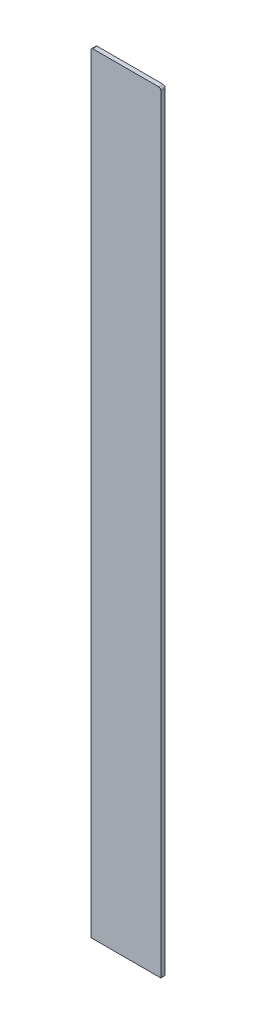
SolidWorks part; units mm, degrees
ref_plane "Front Plane" through (0, 0, 0) normal (0, 0, 1) x (1, 0, 0)
ref_plane "Top Plane" through (0, 0, 0) normal (0, 1, 0) x (1, 0, 0)
ref_plane "Right Plane" through (0, 0, 0) normal (1, 0, 0) x (0, 0, -1)
sketch "Sketch1" plane through (0, 0, 0) normal (0, 0, 1) x (1, 0, 0)
  line L0 (-2.75, -2.75) -> (-2.75, -84)
  line L1 (-2.75, -2.75) -> (2.75, -2.75)
  line L2 (-2.75, -2.75) -> (-2.75, 2.75)
  line L3 (-2.75, 2.75) -> (2.75, 2.75)
  line L4 (2.75, -2.75) -> (2.75, 2.75)
  line L5 (-2.75, -2.75) -> (2.75, 2.75) construction
  line L6 (-2.75, 2.75) -> (2.75, -2.75) construction
  line L7 (-4, -4) -> (4, -4)
  line L8 (-4, -4) -> (-4, 4)
  line L9 (-4, 4) -> (4, 4)
  line L10 (4, -4) -> (4, 4)
  line L11 (-4, -4) -> (4, 4) construction
  line L12 (-4, 4) -> (4, -4) construction
  line L13 (-4, -4) -> (4, -4)
  line L14 (-4, -4) -> (-4, -84)
  line L15 (-4, -84) -> (4, -84)
  line L16 (4, -4) -> (4, -84)
  line L17 (2.75, -2.75) -> (2.75, -84)
  point P0 (0, 0)
  point P5 (0, 0)
  dimension "D1" = 5.5
  dimension "D2" = 8
  dimension "D3" = 80
  dimension "D4" = 8
extrude "Boss-Extrude1" add sketch "Sketch1" along normal blind 0.105 contours L13 L17 L15 L16 | L4 L17 L13 L10 L9 L8 L7 L0 L2 L3 | L14 L15 L0 L7
fillet "Fillet1" radius 0.25 4 edges at (-4, 4, 0.0525) (4, 4, 0.0525) (-2.75, 2.75, 0.0525) (2.75, 2.75, 0.0525)
sketch "Sketch2" plane through (0, 0, 0) normal (0, 0, -1) x (-1, 0, 0)
  line L0 (-2.75, -84) -> (2.75, -84)
  line L8 (4, -84) -> (4, 3.75)
  line L9 (3.75, 4) -> (-3.75, 4)
  line L10 (-4, 3.75) -> (-4, -84)
  line L11 (-4, -84) -> (-2.75, -84)
  line L12 (-2.75, -84) -> (-2.75, 2.5)
  line L13 (-2.5, 2.75) -> (2.5, 2.75)
  line L14 (2.75, 2.5) -> (2.75, -84)
  line L15 (2.75, -84) -> (4, -84)
  line L16 (4, -84) -> (4, 3.75)
  line L17 (3.75, 4) -> (-3.75, 4)
  line L18 (-4, 3.75) -> (-4, -84)
  line L19 (-4, -84) -> (-2.75, -84)
  line L20 (-2.75, -84) -> (-2.75, 2.5)
  line L21 (-2.5, 2.75) -> (2.5, 2.75)
  line L22 (2.75, 2.5) -> (2.75, -84)
  line L23 (2.75, -84) -> (4, -84)
  arc A4 (4, 3.75) -> (3.75, 4) centre (3.75, 3.75) ccw
  arc A5 (-3.75, 4) -> (-4, 3.75) centre (-3.75, 3.75) ccw
  arc A6 (-2.5, 2.75) -> (-2.75, 2.5) centre (-2.5, 2.5) ccw
  arc A7 (2.75, 2.5) -> (2.5, 2.75) centre (2.5, 2.5) ccw
  arc A8 (4, 3.75) -> (3.75, 4) centre (3.75, 3.75) ccw
  arc A9 (-3.75, 4) -> (-4, 3.75) centre (-3.75, 3.75) ccw
  arc A10 (-2.5, 2.75) -> (-2.75, 2.5) centre (-2.5, 2.5) ccw
  arc A11 (2.75, 2.5) -> (2.5, 2.75) centre (2.5, 2.5) ccw
  line M13 (4, -84) -> (4, 3.75)
  arc M14 (4, 3.75) -> (3.75, 4) centre (3.75, 3.75) ccw
  line M15 (3.75, 4) -> (-3.75, 4)
  arc M16 (-3.75, 4) -> (-4, 3.75) centre (-3.75, 3.75) ccw
  line M17 (-4, 3.75) -> (-4, -84)
  line M18 (-4, -84) -> (-2.75, -84)
  line M19 (-2.75, -84) -> (-2.75, 2.5)
  arc M20 (-2.75, 2.5) -> (-2.5, 2.75) centre (-2.5, 2.5) cw
  line M21 (-2.5, 2.75) -> (2.5, 2.75)
  arc M22 (2.5, 2.75) -> (2.75, 2.5) centre (2.5, 2.5) cw
  line M23 (2.75, 2.5) -> (2.75, -84)
  line M24 (2.75, -84) -> (4, -84)
  dimension "D1" = 0
extrude "Boss-Extrude2" add sketch "Sketch2" along normal blind 0.2 contours M24 M13 M14 M15 M16 M17 M18 M19 M20 M21 M22 M23 | L0 M19 M23 M22 M21 M20
sketch "Sketch4" plane through (0, 0, 0.105) normal (0, 0, 1) x (1, 0, 0)
  line L0 (-2.75, -84) -> (2.75, -84)
  line L8 (3.75, 4) -> (-3.75, 4)
  line L9 (-4, 3.75) -> (-4, -84)
  line L10 (-4, -84) -> (-2.75, -84)
  line L11 (-2.75, -84) -> (-2.75, 2.5)
  line L12 (-2.5, 2.75) -> (2.5, 2.75)
  line L13 (2.75, 2.5) -> (2.75, -84)
  line L14 (2.75, -84) -> (4, -84)
  line L15 (4, -84) -> (4, 3.75)
  line L16 (3.75, 4) -> (-3.75, 4)
  line L17 (-4, 3.75) -> (-4, -84)
  line L18 (-4, -84) -> (-2.75, -84)
  line L19 (-2.75, -84) -> (-2.75, 2.5)
  line L20 (-2.5, 2.75) -> (2.5, 2.75)
  line L21 (2.75, 2.5) -> (2.75, -84)
  line L22 (2.75, -84) -> (4, -84)
  line L23 (4, -84) -> (4, 3.75)
  arc A4 (-3.75, 4) -> (-4, 3.75) centre (-3.75, 3.75) ccw
  arc A5 (-2.5, 2.75) -> (-2.75, 2.5) centre (-2.5, 2.5) ccw
  arc A6 (2.75, 2.5) -> (2.5, 2.75) centre (2.5, 2.5) ccw
  arc A7 (4, 3.75) -> (3.75, 4) centre (3.75, 3.75) ccw
  arc A8 (-3.75, 4) -> (-4, 3.75) centre (-3.75, 3.75) ccw
  arc A9 (-2.5, 2.75) -> (-2.75, 2.5) centre (-2.5, 2.5) ccw
  arc A10 (2.75, 2.5) -> (2.5, 2.75) centre (2.5, 2.5) ccw
  arc A11 (4, 3.75) -> (3.75, 4) centre (3.75, 3.75) ccw
  line M13 (3.75, 4) -> (-3.75, 4)
  arc M14 (-3.75, 4) -> (-4, 3.75) centre (-3.75, 3.75) ccw
  line M15 (-4, 3.75) -> (-4, -84)
  line M16 (-4, -84) -> (-2.75, -84)
  line M17 (-2.75, -84) -> (-2.75, 2.5)
  arc M18 (-2.75, 2.5) -> (-2.5, 2.75) centre (-2.5, 2.5) cw
  line M19 (-2.5, 2.75) -> (2.5, 2.75)
  arc M20 (2.5, 2.75) -> (2.75, 2.5) centre (2.5, 2.5) cw
  line M21 (2.75, 2.5) -> (2.75, -84)
  line M22 (2.75, -84) -> (4, -84)
  line M23 (4, -84) -> (4, 3.75)
  arc M24 (4, 3.75) -> (3.75, 4) centre (3.75, 3.75) ccw
  dimension "D1" = 0
extrude "Boss-Extrude3" add sketch "Sketch4" along normal blind 0.2 contours M24 M13 M14 M15 M16 M17 M18 M19 M20 M21 M22 M23 | L0 M17 M21 M20 M19 M18
